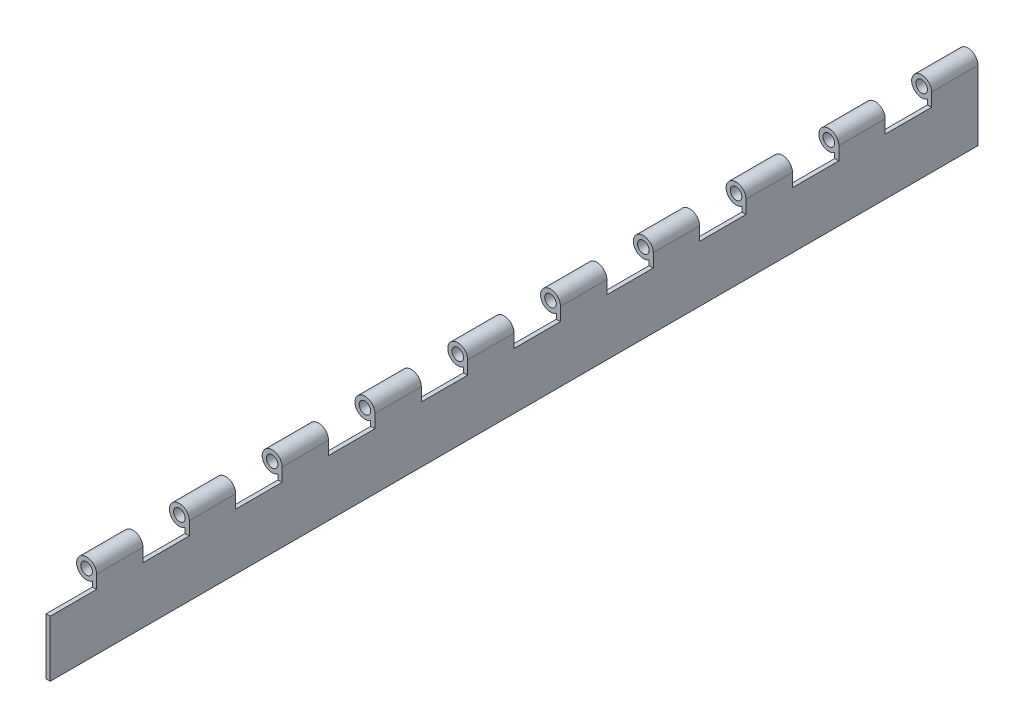
SolidWorks part; units mm, degrees
material "6061 Alloy"
ref_plane "Front Plane" through (0, 0, 0) normal (0, 0, 1) x (1, 0, 0)
ref_plane "Top Plane" through (0, 0, 0) normal (0, 1, 0) x (1, 0, 0)
ref_plane "Right Plane" through (0, 0, 0) normal (1, 0, 0) x (0, 0, -1)
sketch "Sketch1" plane through (0, 0, 0) normal (0, 0, 1) x (1, 0, 0)
  line L0 (5.461, 0) -> (5.461, -38.1)
  line L1 (5.461, -38.1) -> (3.175, -38.1)
  line L2 (3.175, -38.1) -> (3.175, -4.4432)
  circle A0 centre (0, 0) radius 3.175
  arc A1 (5.461, 0) -> (3.175, -4.4432) centre (0, 0) ccw
  circle A2 centre (0, 0) radius 5.461 construction
  dimension "D1" = 6.35
  dimension "D3" = 2.286
  dimension "D4" = 38.1
  dimension "D2" = 2.286
extrude "Boss-Extrude1" add sketch "Sketch1" along normal blind 508
sketch "Sketch2" plane through (5.461, 0, 0) normal (1, 0, 0) x (0, 0, -1)
  line L1 (-508, 5.461) -> (-482.6, 5.461)
  line L2 (-508, 5.461) -> (-508, -7.239)
  line L3 (-508, -7.239) -> (-482.6, -7.239)
  line L4 (-482.6, 5.461) -> (-482.6, -7.239)
  dimension "D1" = 12.7
  dimension "D2" = 25.4
extrude "Cut-Extrude1" cut sketch "Sketch2" against normal through all
pattern_linear "LPattern1" count 10 spacing 50.8 along (0, 0, -1) of "Cut-Extrude1"
